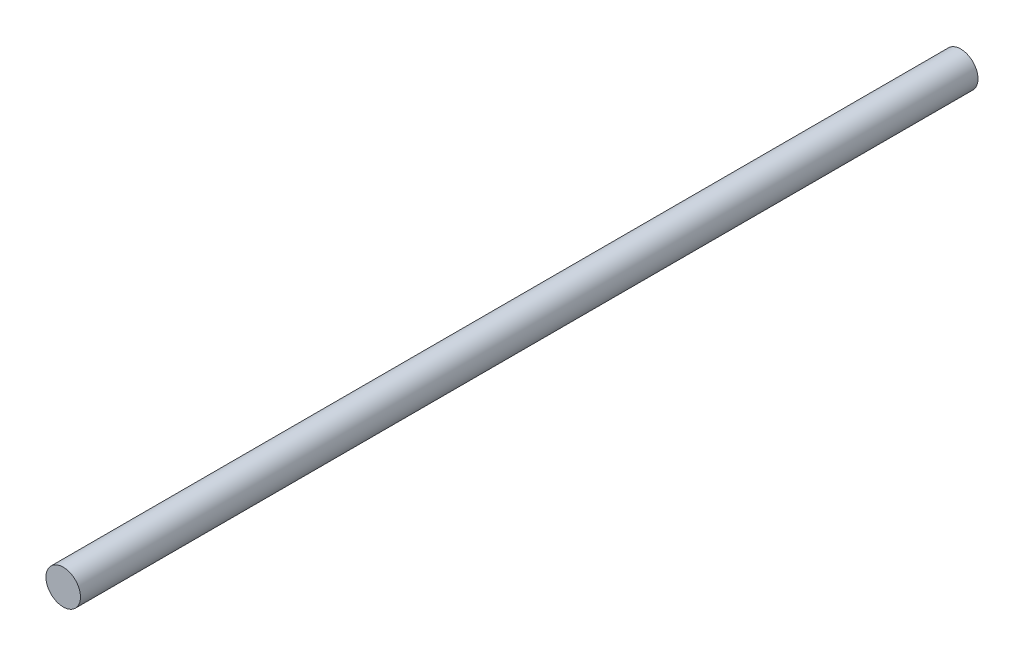
SolidWorks part; units mm, degrees
ref_plane "Plan de face" through (0, 0, 0) normal (0, 0, 1) x (1, 0, 0)
ref_plane "Plan de dessus" through (0, 0, 0) normal (0, 1, 0) x (1, 0, 0)
ref_plane "Plan de droite" through (0, 0, 0) normal (1, 0, 0) x (0, 0, -1)
sketch "Esquisse1" plane through (0, 0, 0) normal (0, 0, 1) x (1, 0, 0)
  circle A0 centre (-19.0148, 7.4977) radius 5
  dimension "D1" = 10
extrude "Boss.-Extru.2" add sketch "Esquisse1" along normal blind 260
